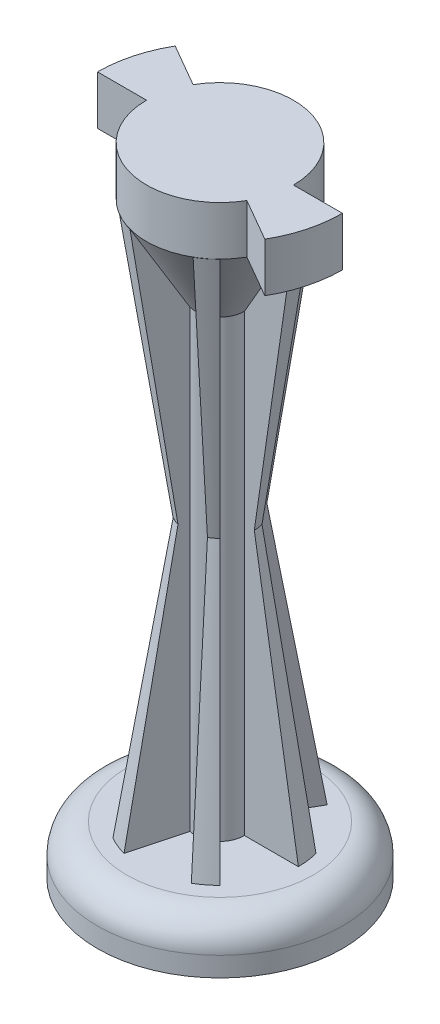
SolidWorks part; units mm, degrees
ref_plane "Front Plane" through (0, 0, 0) normal (0, 0, 1) x (1, 0, 0)
ref_plane "Top Plane" through (0, 0, 0) normal (0, 1, 0) x (1, 0, 0)
ref_plane "Right Plane" through (0, 0, 0) normal (1, 0, 0) x (0, 0, -1)
sketch "Sketch1" plane through (0, 0, 0) normal (0, 1, 0) x (1, 0, 0)
  circle A0 centre (0, 0) radius 12.5
  dimension "D1" = 25
extrude "Boss-Extrude1" add sketch "Sketch1" along normal blind 5 contours A0
sketch "Sketch2" plane through (0, 5, 0) normal (0, 1, 0) x (1, 0, 0)
  circle A0 centre (0, 0) radius 2.5
  dimension "D1" = 5
extrude "Boss-Extrude2" add sketch "Sketch2" along normal blind 60
sketch "Sketch3" plane through (0, 65, 0) normal (0, 1, 0) x (1, 0, 0)
  line L0 (2.5, 0) -> (12.5, 0)
  line L1 (2.1651, -1.25) -> (10.8253, -6.25)
  line L2 (-2.1651, 1.25) -> (-10.8253, 6.25)
  line L3 (-2.5, 0) -> (-12.5, 0)
  line L4 (2.1651, -1.25) -> (0, 0) construction
  line L5 (2.5, 0) -> (0, 0) construction
  arc A0 (-10.8253, 6.25) -> (-12.5, 0) centre (0, 0) ccw
  arc A1 (-2.5, 0) -> (2.1651, -1.25) centre (0, 0) ccw
  circle A2 centre (0, 0) radius 2.5 construction
  arc A3 (10.8253, -6.25) -> (12.5, 0) centre (0, 0) ccw
  arc A4 (2.5, 0) -> (-2.1651, 1.25) centre (0, 0) ccw
  dimension "D1" = 25
  dimension "D2" = 30
extrude "Boss-Extrude3" add sketch "Sketch3" against normal blind 5
sketch "Sketch6" plane through (0, 0, 0) normal (0, 0, 1) x (1, 0, 0)
  line L1 (8, 5) -> (3.5, 32.4911)
  line L5 (0, 5) -> (0, 59.9822)
  line L6 (3.5, 32.4911) -> (7.5, 59.9822)
  line L8 (12.5, 5) -> (-12.5, 5) construction
  line L9 (8, 5) -> (0, 5)
  line L11 (7.5, 59.9822) -> (0, 59.9822)
  point P2 (0, 65)
  point P3 (0, 0)
  point P4 (0, 32.4911)
  point P10 (3.5455, 32.4911)
  point P12 (0, 0)
  point P14 (0, 59.9822)
  dimension "D1" = 8
  dimension "D2" = 7.5
  dimension "D3" = 54.9822
  dimension "D4" = 7.5
  dimension "D5" = 3.5
revolve "Revolve1" add sketch "Sketch6" angle 15 about L5
sketch "Sketch7" plane through (0, 65, 0) normal (0, 1, 0) x (1, 0, 0)
  circle A0 centre (0, 0) radius 7.5
  dimension "D1" = 15
extrude "Boss-Extrude4" add sketch "Sketch7" against normal blind 5
pattern_circular "CirPattern1" count 6 over 360 about axis through (0, 0, 0) along (0, 1, 0) of "Revolve1"
fillet "Fillet1" radius 3 1 edges at (0, 5, 12.5)
sketch "Sketch8" plane through (0, 60, 0) normal (0, -1, 0) x (-1, 0, 0)
  circle A0 centre (0, 0) radius 7.5
  arc A1 (6.4952, 3.75) -> (-7.5, 0) centre (0, 0) ccw construction
extrude "Boss-Extrude5" add sketch "Sketch8" along normal blind 10 draft 30
